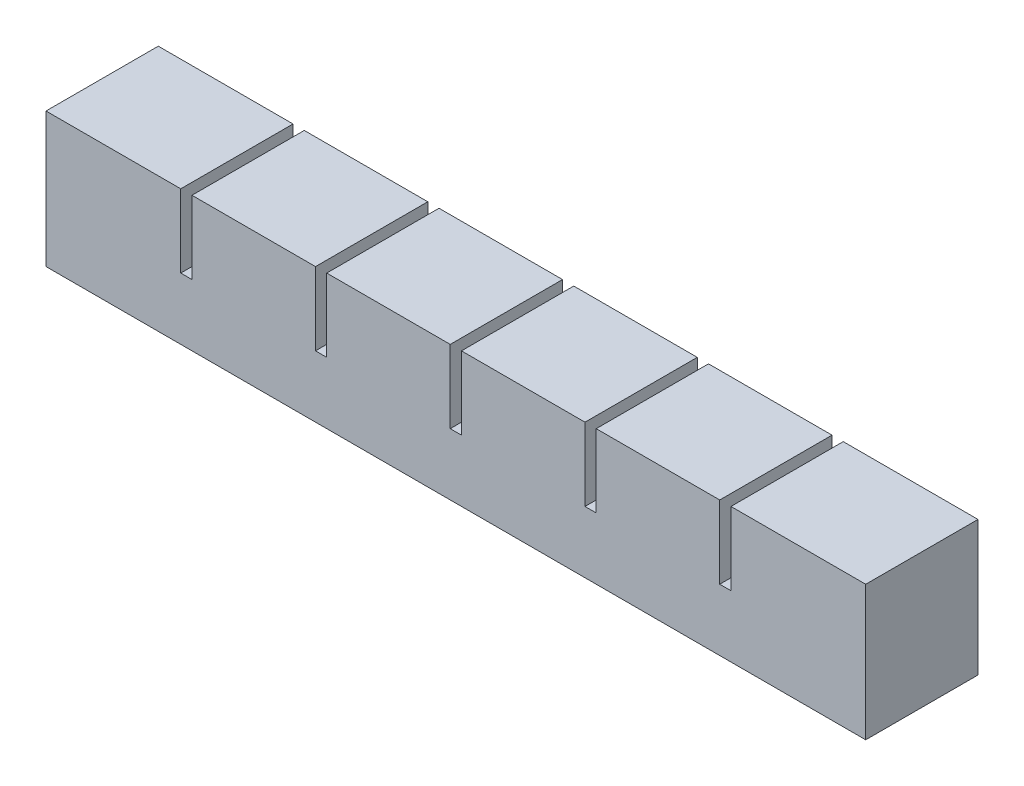
SolidWorks part; units mm, degrees
ref_plane "Front Plane" through (0, 0, 0) normal (0, 0, 1) x (1, 0, 0)
ref_plane "Top Plane" through (0, 0, 0) normal (0, 1, 0) x (1, 0, 0)
ref_plane "Right Plane" through (0, 0, 0) normal (1, 0, 0) x (0, 0, -1)
sketch "Sketch1" plane through (0, 0, 0) normal (0, 0, 1) x (1, 0, 0)
  line L1 (0, 0) -> (22, 0)
  line L2 (0, 0) -> (0, 18)
  line L3 (0, 18) -> (22, 18)
  line L4 (22, 0) -> (22, 18)
  dimension "D1" = 22
  dimension "D2" = 18
extrude "Boss-Extrude1" add sketch "Sketch1" along normal blind 20
sketch "Sketch2" plane through (0, 0, 0) normal (0, -1, 0) x (1, 0, 0)
  line L0 (22, 20) -> (22, 0) construction
  line L1 (5, 15) -> (17, 15)
  line L2 (5, 15) -> (5, 5)
  line L3 (5, 5) -> (17, 5)
  line L4 (17, 15) -> (17, 5)
  line L5 (0, 20) -> (22, 20) construction
  line L6 (0, 20) -> (0, 0) construction
  line L7 (0, 0) -> (22, 0) construction
  dimension "D1" = 5
  dimension "D2" = 5
  dimension "D3" = 5
  dimension "D4" = 5
extrude "Cut-Extrude1" cut sketch "Sketch2" against normal blind 13
sketch "Sketch3" plane through (22, 0, 0) normal (1, 0, 0) x (0, 0, -1)
  line L0 (0, 0) -> (0, 18) construction
  line L1 (-20, 0) -> (0, 0)
  line L2 (-20, 0) -> (-20, 5)
  line L3 (-20, 5) -> (0, 5)
  line L4 (0, 0) -> (0, 5)
  dimension "D1" = 5
extrude "Boss-Extrude2" add sketch "Sketch3" along normal blind 2
pattern_linear "LPattern1" count 6 spacing 24 along (1, 0, 0) of bodies 103
sketch "Sketch4" plane through (142, 0, 0) normal (1, 0, 0) x (0, 0, -1)
  line L1 (-20, 5) -> (0, 5)
  line L2 (-20, 5) -> (-20, 18)
  line L3 (-20, 18) -> (0, 18)
  line L4 (0, 5) -> (0, 18)
extrude "Boss-Extrude3" add sketch "Sketch4" along normal up to surface (2 mm away) up to face at (144, 2.5, 10)
sketch "Sketch5" plane through (0, 0, 0) normal (-1, 0, 0) x (0, 0, 1)
  line L1 (0, 0) -> (20, 0)
  line L2 (0, 0) -> (0, 18)
  line L3 (0, 18) -> (20, 18)
  line L4 (20, 0) -> (20, 18)
extrude "Boss-Extrude4" add sketch "Sketch5" along normal blind 2
combine bodies "Combine1" operation type add bodies to combine 104 105 106 107 109 110
ref_point "Point1"
sketch "Sketch6" plane through (0, 0, 0) normal (0, -1, 0) x (-1, 0, 0)
  line L0 (-137, -5) -> (-137, -15) construction
  line L1 (-5, -9) -> (-137, -9)
  line L2 (-5, -9) -> (-5, -11)
  line L3 (-5, -11) -> (-137, -11)
  line L4 (-137, -9) -> (-137, -11)
  line L5 (-5, -9) -> (-137, -11) construction
  line L6 (-5, -11) -> (-137, -9) construction
  point P0 (-71, -10)
  dimension "D1" = 2
extrude "Cut-Extrude2" cut sketch "Sketch6" against normal blind 2
sketch "Sketch7" plane through (0, 0, 0) normal (0, -1, 0) x (-1, 0, 0)
  line L1 (2, -20) -> (-144, -20)
  line L2 (2, -20) -> (2, 0)
  line L3 (2, 0) -> (-144, 0)
  line L4 (-144, -20) -> (-144, 0)
extrude "Boss-Extrude5" add sketch "Sketch7" along normal blind 6
